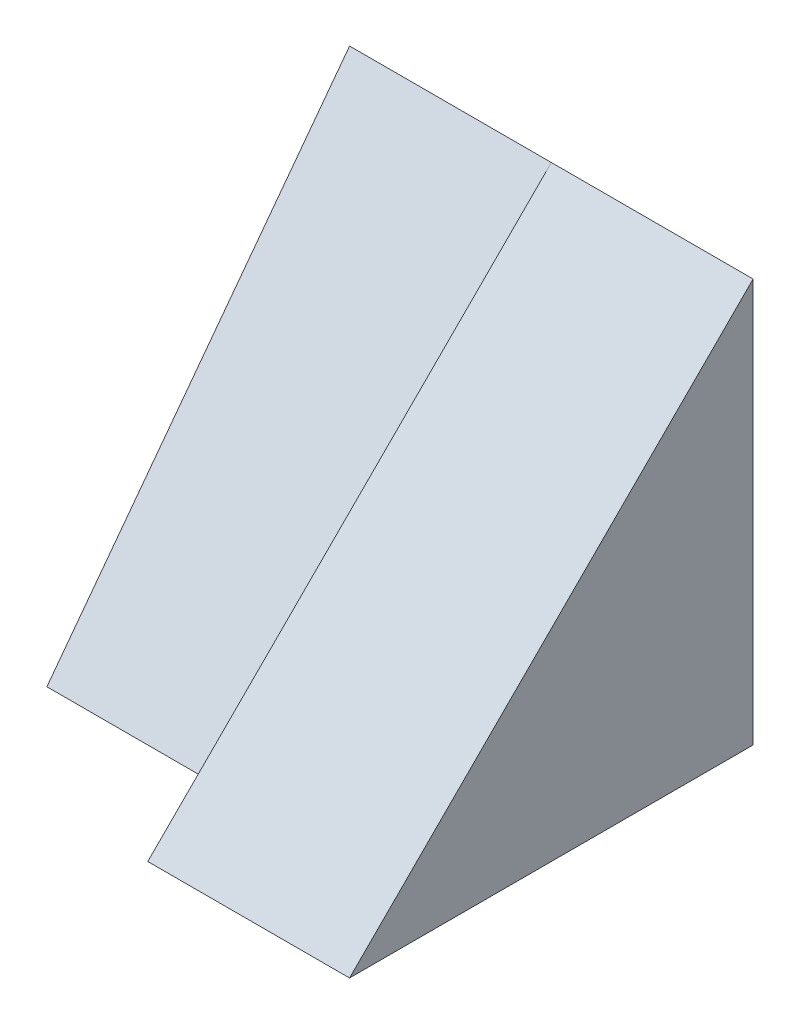
SolidWorks part; units mm, degrees
ref_plane "Front Plane" through (0, 0, 0) normal (0, 0, 1) x (1, 0, 0)
ref_plane "Top Plane" through (0, 0, 0) normal (0, 1, 0) x (1, 0, 0)
ref_plane "Right Plane" through (0, 0, 0) normal (1, 0, 0) x (0, 0, -1)
sketch "Sketch1" plane through (0, 0, 0) normal (1, 0, 0) x (0, 0, -1)
  line L1 (0, 0) -> (4, 0)
  line L2 (0, 0) -> (0, 4)
  line L3 (0, 4) -> (4, 4)
  line L4 (4, 0) -> (4, 4)
  dimension "D1" = 4
  dimension "D2" = 4
extrude "Boss-Extrude1" add sketch "Sketch1" along normal blind 2
sketch "Sketch2" plane through (0, 0, 0) normal (-1, 0, 0) x (0, 0, 1)
  line L0 (-1, 0) -> (-1, 4)
  line L1 (0, 0) -> (-4, 0) construction
  line L2 (-4, 0) -> (-4, 4) construction
  line L3 (-4, 4) -> (-4, 0)
  line L4 (-4, 0) -> (-1, 0)
  line L5 (-4, 4) -> (0, 4) construction
  line L6 (-1, 4) -> (-4, 4)
  dimension "D1" = 3
  dimension "D2" = 4
extrude "Boss-Extrude2" add sketch "Sketch2" along normal blind 2
sketch "Sketch3" plane through (2, 0, 0) normal (1, 0, 0) x (0, 0, -1)
  line L0 (0, 0) -> (4, 4)
  line L1 (4, 4) -> (0, 4)
  line L2 (0, 4) -> (0, 0)
extrude "Cut-Extrude1" cut sketch "Sketch3" against normal blind 2
sketch "Sketch4" plane through (-2, 0, 0) normal (-1, 0, 0) x (0, 0, 1)
  line L0 (-1, 0) -> (-4, 4)
  line L1 (-4, 4) -> (-1, 4)
  line L2 (-1, 4) -> (-1, 0)
extrude "Cut-Extrude2" cut sketch "Sketch4" against normal blind 2
